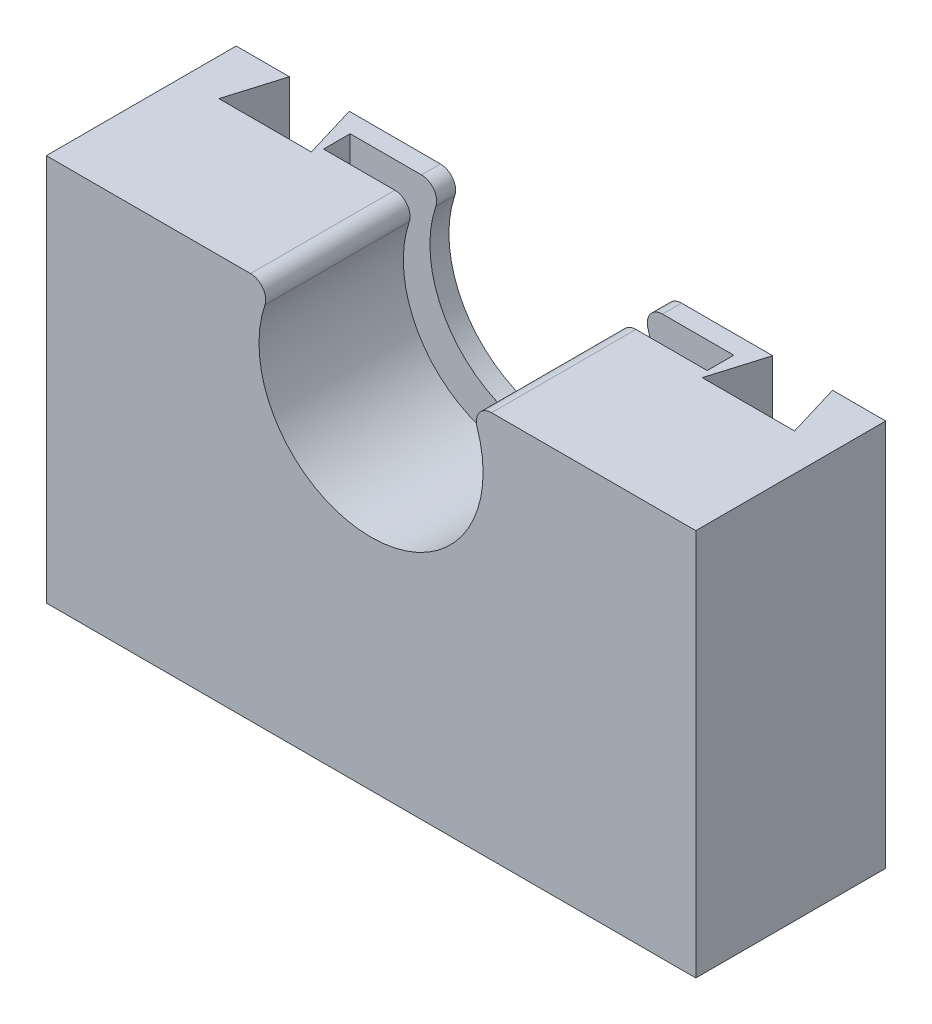
SolidWorks part; units mm, degrees
ref_plane "Front Plane" through (0, 0, 0) normal (0, 0, 1) x (1, 0, 0)
ref_plane "Top Plane" through (0, 0, 0) normal (0, 1, 0) x (1, 0, 0)
ref_plane "Right Plane" through (0, 0, 0) normal (1, 0, 0) x (0, 0, -1)
sketch "Sketch2" plane through (0, 0, 0) normal (0, 0, 1) x (1, 0, 0)
  line L0 (11.1505, 5.8899) -> (11.1505, -22.9851) construction
  line L1 (53.9005, 28.0149) -> (27.0147, 28.0149)
  line L2 (53.9005, 28.0149) -> (53.9005, -22.9851)
  line L3 (53.9005, -22.9851) -> (-31.5995, -22.9851)
  line L4 (-31.5995, 28.0149) -> (-31.5995, -22.9851)
  line L5 (-31.5995, 2.5149) -> (53.9005, 2.5149) construction
  line L6 (-4.7137, 28.0149) -> (-31.5995, 28.0149)
  line L7 (11.1505, 20.6399) -> (11.1505, -22.9851) construction
  line L8 (11.1505, 20.6399) -> (25.1204, 25.3731) construction
  line L9 (-3.5995, 20.6399) -> (25.9005, 20.6399) construction
  arc A0 (-2.8194, 25.3731) -> (25.1204, 25.3731) centre (11.1505, 20.6399) ccw
  arc A1 (-4.7137, 28.0149) -> (-2.8194, 25.3731) centre (-4.7137, 26.0149) cw
  arc A2 (27.0147, 28.0149) -> (25.1204, 25.3731) centre (27.0147, 26.0149) ccw
  dimension "D4" = 2
  dimension "D5" = 29.5
  dimension "D3" = 2
  dimension "D1" = 85.5
  dimension "D2" = 51
extrude "Boss-Extrude1" add sketch "Sketch2" along normal blind 25
sketch "Sketch5" plane through (0, 0, 25) normal (0, 0, 1) x (1, 0, 0)
  line L0 (11.1505, 5.8899) -> (11.1505, 1.4899) construction
  line L1 (-31.5995, -22.9851) -> (53.9005, -22.9851) construction
  line L2 (11.1505, 5.8899) -> (11.1505, 1.4899)
  line L3 (11.1505, -7.3101) -> (11.1505, -22.9851) construction
  arc A0 (-2.8194, 25.3731) -> (25.1204, 25.3731) centre (11.1505, 20.6399) ccw construction
  circle A1 centre (11.1505, -2.9101) radius 4.4
  dimension "D2" = 8.8
  dimension "D1" = 8.8
extrude "Cut-Extrude3" cut sketch "Sketch5" along normal blind 4.8 from surface at -25 contours A1 starting at face at (11.1505, 12.2907, 0)
sketch "Sketch6" plane through (0, 28.0149, 0) normal (0, 1, 0) x (1, 0, 0)
  line L0 (-24.5995, 0) -> (-26.7385, -7.1363)
  line L1 (-4.7137, 0) -> (-31.5995, 0) construction
  line L2 (-26.7385, -7.1363) -> (-14.5747, -7.1363)
  line L3 (-14.5747, -7.1363) -> (-16.7137, 0)
  line L7 (-31.5995, -25) -> (-31.5995, 0) construction
  line L13 (46.9005, 0) -> (49.0401, -7.1362)
  line L14 (49.0401, -7.1362) -> (36.8751, -7.1362)
  line L15 (36.8751, -7.1362) -> (39.0147, 0)
  line L16 (53.9005, 0) -> (27.0147, 0) construction
  line L19 (53.9005, -25) -> (53.9005, 0) construction
  line L30 (-24.5995, 0) -> (-16.7137, 0)
  line L31 (39.0147, 0) -> (46.9005, 0)
  line L32 (-4.7137, -25) -> (-4.7137, 0) construction
  line L33 (27.0147, -25) -> (27.0147, 0) construction
  dimension "D3" = 7.45
  dimension "D4" = 7.45
  dimension "D5" = 106.685
  dimension "D6" = 12.1639
  dimension "D7" = 7
  dimension "D8" = 7
  dimension "D9" = 73.31
  dimension "D10" = 106.69
  dimension "D11" = 12
  dimension "D12" = 12
  dimension "D21" = 7.45
  dimension "D23" = 7.45
extrude "Cut-Extrude4" cut sketch "Sketch6" against normal blind 25
ref_plane "Plane1" through (0, 0, 2.5) normal (0, 0, -1) x (-1, 0, 0)
sketch "Sketch8" plane through (0, 0, 2.5) normal (0, 0, -1) x (-1, 0, 0)
  line L0 (-27.0147, 28.0149) -> (4.7137, 28.0149) construction
  line L1 (-11.1505, 28.0149) -> (-11.1505, -7.3101) construction
  line L2 (-36.4005, 2.9448) -> (14.0995, 2.9448)
  line L3 (-36.4005, 2.9448) -> (-36.4005, 28.0149)
  line L4 (-39.0147, 28.0149) -> (-27.0147, 28.0149) construction
  line L5 (-36.4005, 28.0149) -> (14.0995, 28.0149)
  line L6 (4.7137, 28.0149) -> (16.7137, 28.0149) construction
  line L7 (14.0995, 28.0149) -> (14.0995, 2.9448)
  circle A0 centre (-11.1505, -2.9101) radius 4.4 construction
  point P11 (-11.1505, 2.9448)
extrude "Cut-Extrude5" cut sketch "Sketch8" against normal blind 3.5
